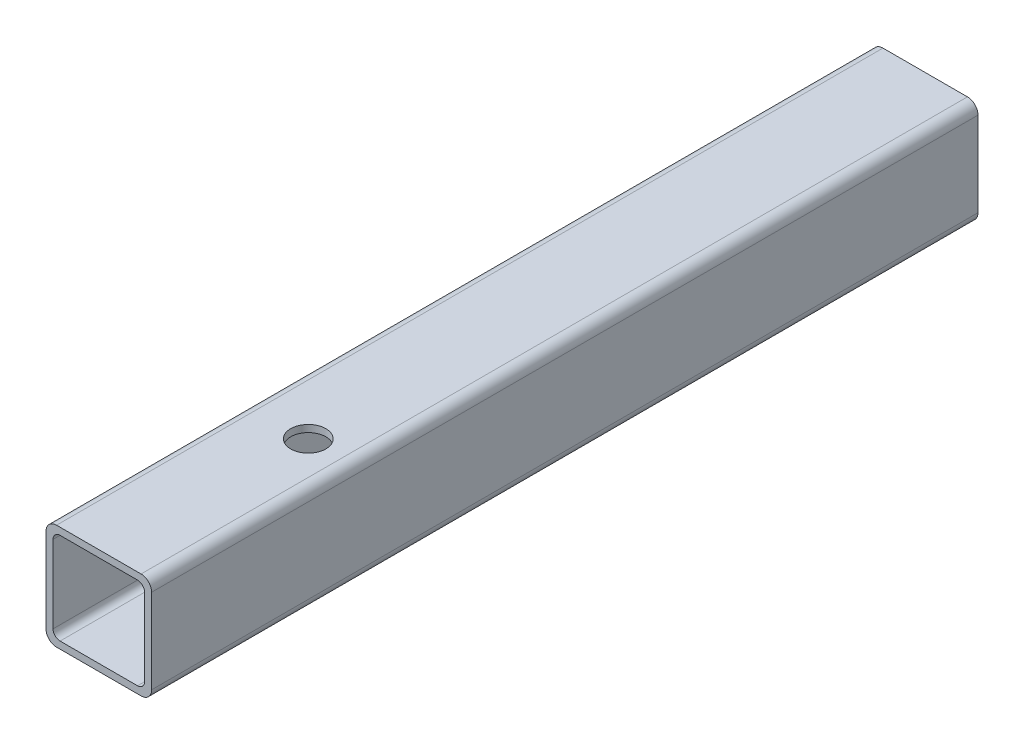
SolidWorks part; units mm, degrees
material "AISI 1020"
ref_plane "Спереди" through (0, 0, 0) normal (0, 0, 1) x (1, 0, 0)
ref_plane "Сверху" through (0, 0, 0) normal (0, 1, 0) x (1, 0, 0)
ref_plane "Справа" through (0, 0, 0) normal (1, 0, 0) x (0, 0, -1)
sketch "Эскиз1" plane through (0, 0, 0) normal (0, 0, 1) x (1, 0, 0)
  point P0 (0, 0)
  line B0 (-12, 0) -> (12, 0)
  line B1 (-15, -3) -> (-15, -27)
  line B2 (-12, -30) -> (12, -30)
  line B3 (15, -3) -> (15, -27)
  line B4 (-11, -2) -> (11, -2)
  line B5 (-13, -4) -> (-13, -26)
  line B6 (-11, -28) -> (11, -28)
  line B7 (13, -4) -> (13, -26)
  arc B8 (-15, -27) -> (-12, -30) centre (-12, -27) ccw
  arc B9 (12, -30) -> (15, -27) centre (12, -27) ccw
  arc B10 (12, 0) -> (15, -3) centre (12, -3) cw
  arc B11 (-12, 0) -> (-15, -3) centre (-12, -3) ccw
  arc B12 (-13, -26) -> (-11, -28) centre (-11, -26) ccw
  arc B13 (11, -28) -> (13, -26) centre (11, -26) ccw
  arc B14 (11, -2) -> (13, -4) centre (11, -4) cw
  arc B15 (-11, -2) -> (-13, -4) centre (-11, -4) ccw
sketch_block_instance "Блок-30х30х2-1"
sketch_block "Блок-30х30х2" parameters "D3"=3, "D4"=2, "D1"=30, "D2"=2
extrude "Бобышка-Вытянуть1" add sketch "Эскиз1" against normal up to surface (234.7332 mm away)
sketch "Эскиз2" plane through (0, 0, 0) normal (0, 1, 0) x (1, 0, 0)
  circle A0 centre (2.5, 57) radius 5 construction
  circle A1 centre (2.5, 57) radius 5
extrude "Вырез-Вытянуть1" cut sketch "Эскиз2" against normal through all
